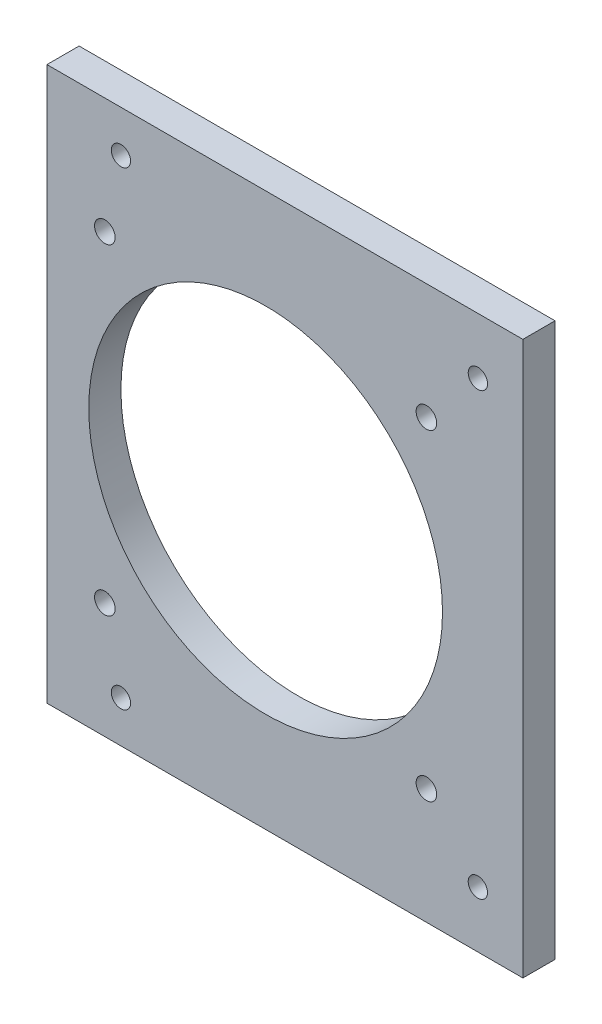
SolidWorks part; units mm, degrees
material "PBT Общее назначение"
ref_plane "Спереди" through (0, 0, 0) normal (0, 0, 1) x (1, 0, 0)
ref_plane "Сверху" through (0, 0, 0) normal (0, 1, 0) x (1, 0, 0)
ref_plane "Справа" through (0, 0, 0) normal (1, 0, 0) x (0, 0, -1)
sketch "Эскиз2" plane through (0, 0, 0) normal (0, 1, 0) x (1, 0, 0)
  line L0 (0, 0) -> (0, -131.0411) construction
  line L1 (0, 0) -> (-67.0136, 0) construction
sketch "Эскиз3" plane through (0, 0, 0) normal (0, 0, 1) x (1, 0, 0)
  line L0 (0, 0) -> (0, 105.2454) construction
sketch "Эскиз1" plane through (0, 0, 81) normal (0, 0, 1) x (1, 0, 0)
  line L0 (2.5, -5) -> (2.5, 95)
  line L1 (-67, -5) -> (-67, 95)
  line L2 (0, 0) -> (-67.0136, 0) construction
  line L3 (0, 0) -> (0, 105.2454) construction
  line L4 (-4.5, 79.25) -> (-4.5, 10.75) construction
  line L9 (2.5, 95) -> (-67, 95)
  line L11 (-67, -5) -> (2.5, -5)
  circle A1 centre (-60, 8.5) radius 1.5
  circle A6 centre (-60, 81.5) radius 1.5
  circle A8 centre (-4.5, 79.25) radius 1.5
  circle A10 centre (-4.5, 10.75) radius 1.5
  dimension "D5" = 7
  dimension "D6" = 7
  dimension "D3" = 3
  dimension "D4" = 13.5
  dimension "D7" = 15.75
  dimension "D8" = 15.75
  dimension "D9" = 7
  dimension "D10" = 13.5
  dimension "D2" = 100
  dimension "D1" = 69.5
  dimension "D11" = 5
  dimension "D12" = 2.5
extrude "Бобышка-Вытянуть1" add sketch "Эскиз1" against normal blind 5
sketch "Эскиз4" plane through (-67, 0, 0) normal (-1, 0, 0) x (0, 0, 1)
  line L0 (76, 95) -> (76, -5) construction
  line L1 (76, 95) -> (66, 95) construction
  line L2 (76, -5) -> (66, -5) construction
  line L3 (66, 95) -> (66, -5) construction
  dimension "D1" = 10
sketch "Эскиз5" plane through (0, 0, 81) normal (0, 0, 1) x (1, 0, 0)
  line L0 (-37.5, 73.2) -> (-37.5, 16.8) construction
  line L1 (-9.3, 45) -> (-65.7, 45) construction
  line L3 (-62.5, 70) -> (-12.5, 70) construction
  line L4 (-62.5, 70) -> (-62.5, 20) construction
  line L5 (-62.5, 20) -> (-12.5, 20) construction
  line L6 (-12.5, 70) -> (-12.5, 20) construction
  line L7 (-62.5, 70) -> (-12.5, 20) construction
  line L8 (-62.5, 20) -> (-12.5, 70) construction
  line L24 (-63.7, 26.06) -> (-61.07, 26.06) construction
  line L25 (-56.44, 21.43) -> (-56.44, 18.8) construction
  line L26 (-54.44, 16.8) -> (-20.56, 16.8) construction
  line L27 (-18.56, 18.8) -> (-18.56, 21.43) construction
  line L28 (-13.93, 26.06) -> (-11.3, 26.06) construction
  line L29 (-9.3, 28.06) -> (-9.3, 61.94) construction
  line L30 (-11.3, 63.94) -> (-13.93, 63.94) construction
  line L31 (-18.56, 68.57) -> (-18.56, 71.2) construction
  line L32 (-20.56, 73.2) -> (-54.44, 73.2) construction
  line L33 (-56.44, 71.2) -> (-56.44, 68.57) construction
  line L34 (-61.07, 63.94) -> (-63.7, 63.94) construction
  line L35 (-65.7, 61.94) -> (-65.7, 28.06) construction
  circle A0 centre (-12.5, 70) radius 1.6
  circle A1 centre (-12.5, 20) radius 1.6
  circle A2 centre (-62.5, 20) radius 1.6
  circle A3 centre (-62.5, 70) radius 1.6
  circle A4 centre (-37.5, 45) radius 27.5
  arc A24 (-65.7, 28.06) -> (-63.7, 26.06) centre (-63.7, 28.06) ccw construction
  arc A25 (-56.44, 21.43) -> (-61.07, 26.06) centre (-61.07, 21.43) ccw construction
  arc A26 (-56.44, 18.8) -> (-54.44, 16.8) centre (-54.44, 18.8) ccw construction
  arc A27 (-20.56, 16.8) -> (-18.56, 18.8) centre (-20.56, 18.8) ccw construction
  arc A28 (-13.93, 26.06) -> (-18.56, 21.43) centre (-13.93, 21.43) ccw construction
  arc A29 (-11.3, 26.06) -> (-9.3, 28.06) centre (-11.3, 28.06) ccw construction
  arc A30 (-9.3, 61.94) -> (-11.3, 63.94) centre (-11.3, 61.94) ccw construction
  arc A31 (-18.56, 68.57) -> (-13.93, 63.94) centre (-13.93, 68.57) ccw construction
  arc A32 (-18.56, 71.2) -> (-20.56, 73.2) centre (-20.56, 71.2) ccw construction
  arc A33 (-54.44, 73.2) -> (-56.44, 71.2) centre (-54.44, 71.2) ccw construction
  arc A34 (-61.07, 63.94) -> (-56.44, 68.57) centre (-61.07, 68.57) ccw construction
  arc A35 (-63.7, 63.94) -> (-65.7, 61.94) centre (-63.7, 61.94) ccw construction
  point P11 (-37.5, 45)
  dimension "D4" = 3.2
  dimension "D5" = 55
  dimension "D2" = 50
  dimension "D3" = 50
extrude "Вырез-Вытянуть1" cut sketch "Эскиз5" against normal through all
sketch "Эскиз6" plane through (-67, 0, 0) normal (-1, 0, 0) x (0, 0, 1)
  line L4 (81, -5) -> (81, 95)
  line L5 (81, 95) -> (76, 95)
  line L6 (76, 95) -> (76, -5)
  line L7 (76, -5) -> (81, -5)
  line L8 (81, -5) -> (81, 95)
  line L9 (81, 95) -> (76, 95)
  line L10 (76, 95) -> (76, -5)
  line L11 (76, -5) -> (81, -5)
  dimension "D1" = 0
extrude "Бобышка-Вытянуть2" add sketch "Эскиз6" along normal blind 4.5
sketch "Эскиз7" plane through (0, 95, 0) normal (0, 1, 0) x (1, 0, 0)
  line L4 (-71.5, -81) -> (2.5, -81)
  line L5 (2.5, -81) -> (2.5, -76)
  line L6 (2.5, -76) -> (-71.5, -76)
  line L7 (-71.5, -76) -> (-71.5, -81)
  line L8 (-71.5, -81) -> (2.5, -81)
  line L9 (2.5, -81) -> (2.5, -76)
  line L10 (2.5, -76) -> (-71.5, -76)
  line L11 (-71.5, -76) -> (-71.5, -81)
  dimension "D1" = 0
extrude "Вырез-Вытянуть2" cut sketch "Эскиз7" against normal blind 7
sketch "Эскиз8" plane through (0, -5, 0) normal (0, -1, 0) x (1, 0, 0)
  line L4 (2.5, 81) -> (-71.5, 81)
  line L5 (-71.5, 81) -> (-71.5, 76)
  line L6 (-71.5, 76) -> (2.5, 76)
  line L7 (2.5, 76) -> (2.5, 81)
  line L8 (2.5, 81) -> (-71.5, 81)
  line L9 (-71.5, 81) -> (-71.5, 76)
  line L10 (-71.5, 76) -> (2.5, 76)
  line L11 (2.5, 76) -> (2.5, 81)
  dimension "D1" = 0
extrude "Вырез-Вытянуть3" cut sketch "Эскиз8" against normal blind 7
